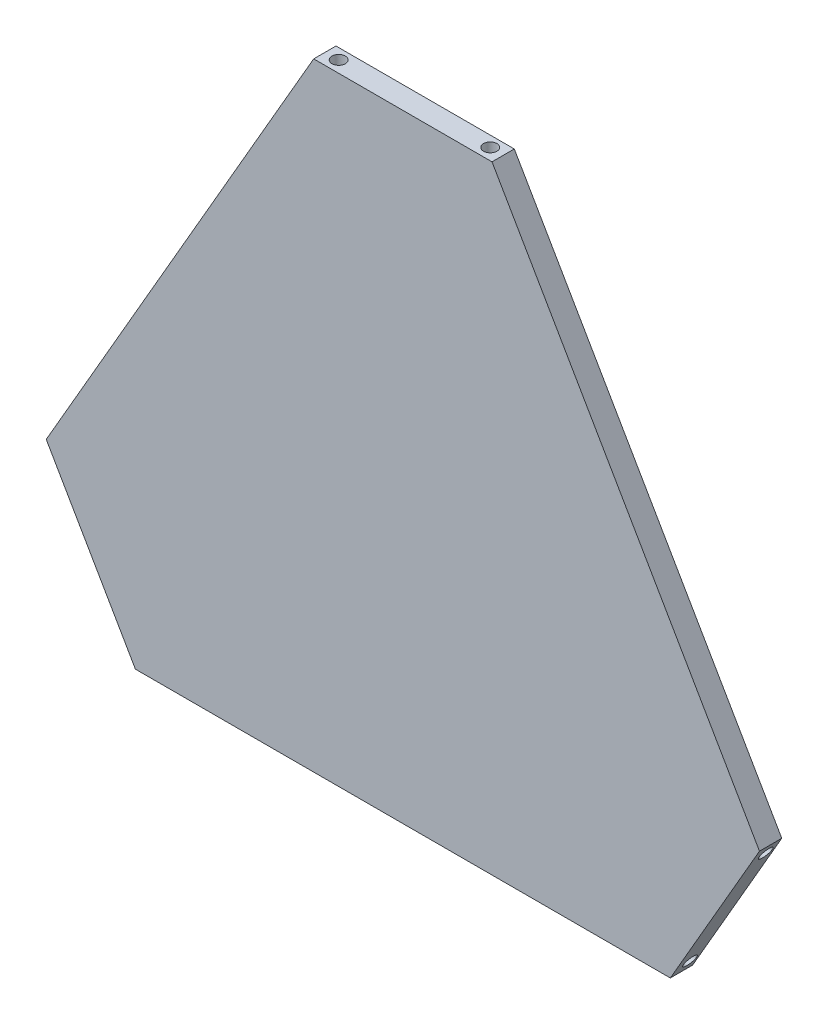
SolidWorks part; units mm, degrees
ref_plane "Front Plane" through (0, 0, 0) normal (0, 0, 1) x (1, 0, 0)
ref_plane "Top Plane" through (0, 0, 0) normal (0, 1, 0) x (1, 0, 0)
ref_plane "Right Plane" through (0, 0, 0) normal (1, 0, 0) x (0, 0, -1)
sketch "Sketch1" plane through (0, 0, 0) normal (0, 0, 1) x (1, 0, 0)
  line L0 (0, 0) -> (120, 0)
  line L1 (120, 0) -> (140, 34.641)
  line L2 (140, 34.641) -> (80, 138.5641)
  line L3 (80, 138.5641) -> (40, 138.5641)
  line L4 (40, 138.5641) -> (-20, 34.641)
  line L5 (-20, 34.641) -> (0, 0)
  dimension "D1" = 120
  dimension "D2" = 40
  dimension "D3" = 120
  dimension "D4" = 120
  dimension "D5" = 120
extrude "Boss-Extrude1" add sketch "Sketch1" along normal blind 5
sketch "Sketch3" plane through (0, 0, 0) normal (-0.866, -0.5, 0) x (0, 0, 1)
  line L0 (5, 40) -> (0, 40) construction
  line L1 (5, 0) -> (0, 0) construction
  circle A0 centre (2.3334, 37) radius 1.5
  circle A1 centre (2.3334, 3) radius 1.5
  dimension "D1" = 3
  dimension "D3" = 3
  dimension "D4" = 3
  dimension "D2" = 3
extrude "Cut-Extrude1" cut sketch "Sketch3" against normal blind 3
sketch "Sketch4" plane through (90, -51.9615, 0) normal (0.866, -0.5, 0) x (0, 0, -1)
  line L0 (-5, 60) -> (0, 60) construction
  line L1 (-5, 100) -> (0, 100) construction
  circle A0 centre (-2.0855, 63) radius 1.5
  circle A1 centre (-2.0855, 97) radius 1.5
  dimension "D1" = 3
  dimension "D2" = 3
  dimension "D3" = 3
  dimension "D4" = 3
extrude "Cut-Extrude2" cut sketch "Sketch4" against normal blind 3
sketch "Sketch5" plane through (0, 138.5641, 0) normal (0, 1, 0) x (1, 0, 0)
  line L0 (80, -5) -> (80, 0) construction
  line L1 (40, -5) -> (40, 0) construction
  circle A0 centre (77, -2.3971) radius 1.5
  circle A1 centre (43, -2.3971) radius 1.5
  dimension "D1" = 3
  dimension "D2" = 3
  dimension "D3" = 3
extrude "Cut-Extrude3" cut sketch "Sketch5" against normal blind 3
sketch "Sketch6" plane through (0, 0, 5) normal (0, 0, 1) x (1, 0, 0)
  line L0 (-10, 17.3205) -> (110, 86.6025)
  line L1 (-20, 34.641) -> (0, 0) construction
  line L2 (140, 34.641) -> (80, 138.5641) construction
  line L3 (130, 17.3205) -> (10, 86.6025)
  line L4 (120, 0) -> (140, 34.641) construction
  line L5 (40, 138.5641) -> (-20, 34.641) construction
  line L6 (60, 0) -> (60, 138.5641)
  line L7 (0, 0) -> (120, 0) construction
  line L8 (80, 138.5641) -> (40, 138.5641) construction
